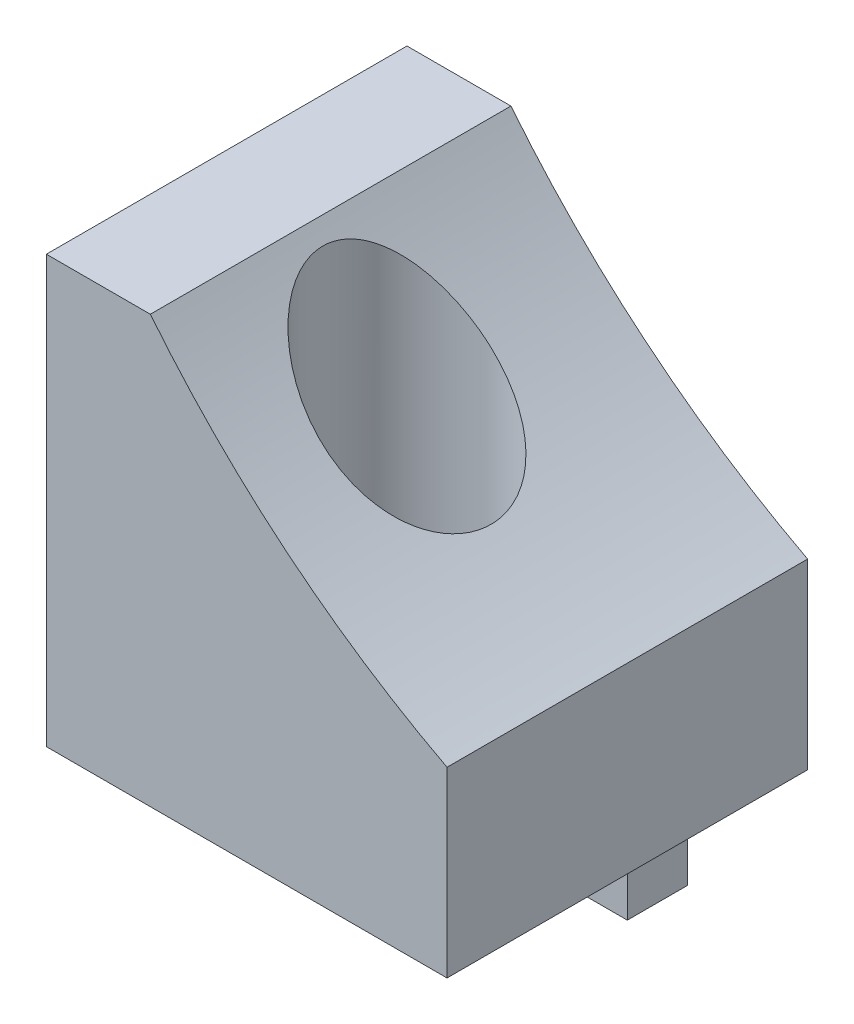
SolidWorks part; units mm, degrees
ref_plane "前视基准面" through (0, 0, 0) normal (0, 0, 1) x (1, 0, 0)
ref_plane "上视基准面" through (0, 0, 0) normal (0, 1, 0) x (1, 0, 0)
ref_plane "右视基准面" through (0, 0, 0) normal (1, 0, 0) x (0, 0, -1)
sketch "草图1" plane through (0, 0, 0) normal (0, 0, 1) x (1, 0, 0)
  line L0 (0, 0) -> (20, 0)
  line L1 (0, 0) -> (0, 21.29)
  line L2 (20, 0) -> (20, 9.1113)
  line L3 (0, 21.29) -> (5.19, 21.29)
  arc A1 (5.19, 21.29) -> (20, 9.1113) centre (41.82, 50.74) ccw
extrude "凸台-拉伸1" add sketch "草图1" along normal blind 18
sketch "草图2" plane through (0, 0, 0) normal (0, -1, 0) x (1, 0, 0)
  circle A0 centre (10, 10) radius 4.2
extrude "切除-拉伸1" cut sketch "草图2" against normal blind 28
sketch "草图3" plane through (0, 0, 0) normal (0, -1, 0) x (1, 0, 0)
  line L0 (10, 0) -> (14, 0)
  line L1 (0, 0) -> (20, 0) construction
  line L2 (10, 0) -> (6, 0)
  line L3 (6, 0) -> (6, 3)
  line L4 (6, 3) -> (14, 3)
  line L5 (14, 3) -> (14, 0)
extrude "凸台-拉伸2" add sketch "草图3" along normal blind 8
sketch "草图4" plane through (0, 0, 3) normal (0, 0, 1) x (1, 0, 0)
  circle A0 centre (10, -3) radius 1.6
extrude "切除-拉伸2" cut sketch "草图4" against normal blind 8
chamfer "倒角1" distance 5 angle 45 1 edges
chamfer "倒角2" distance 5 angle 45 1 edges
